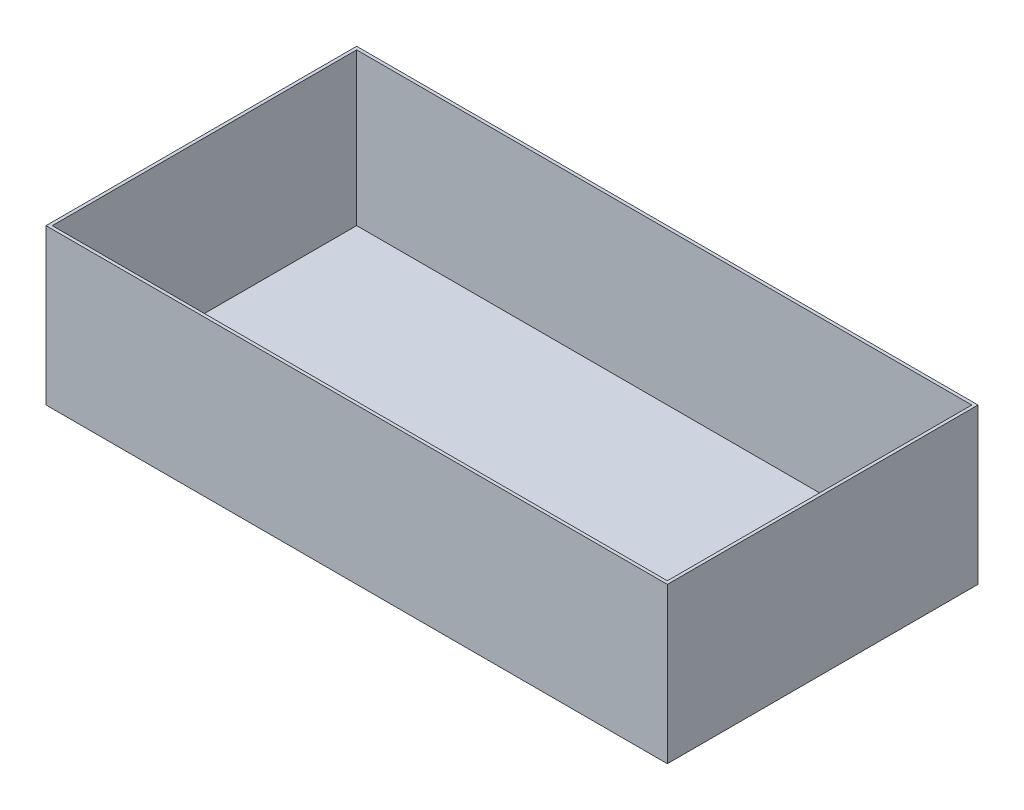
SolidWorks part; units mm, degrees
ref_plane "Front Plane" through (0, 0, 0) normal (0, 0, 1) x (1, 0, 0)
ref_plane "Top Plane" through (0, 0, 0) normal (0, 1, 0) x (1, 0, 0)
ref_plane "Right Plane" through (0, 0, 0) normal (1, 0, 0) x (0, 0, -1)
sketch "Sketch5" plane through (0, 0, 0) normal (0, 1, 0) x (1, 0, 0)
  line L1 (-100, -50) -> (100, -50)
  line L2 (-100, -50) -> (-100, 50)
  line L3 (-100, 50) -> (100, 50)
  line L4 (100, -50) -> (100, 50)
  line L5 (-100, -50) -> (100, 50) construction
  line L6 (-100, 50) -> (100, -50) construction
  point P0 (0, 0)
  point P1 (0, 0)
  dimension "D1" = 200
  dimension "D2" = 100
extrude "Boss-Extrude2" add sketch "Sketch5" along normal blind 50 contours L3 L4 L1 L2
sketch "Sketch6" plane through (0, 50, 0) normal (0, 1, 0) x (1, 0, 0)
  line L1 (-99, -49) -> (99, -49)
  line L2 (-99, -49) -> (-99, 49)
  line L3 (-99, 49) -> (99, 49)
  line L4 (99, -49) -> (99, 49)
  line L5 (-99, -49) -> (99, 49) construction
  line L6 (-99, 49) -> (99, -49) construction
  point P0 (0, 0)
  dimension "D1" = 198
  dimension "D2" = 98
extrude "Cut-Extrude2" cut sketch "Sketch6" against normal blind 49
